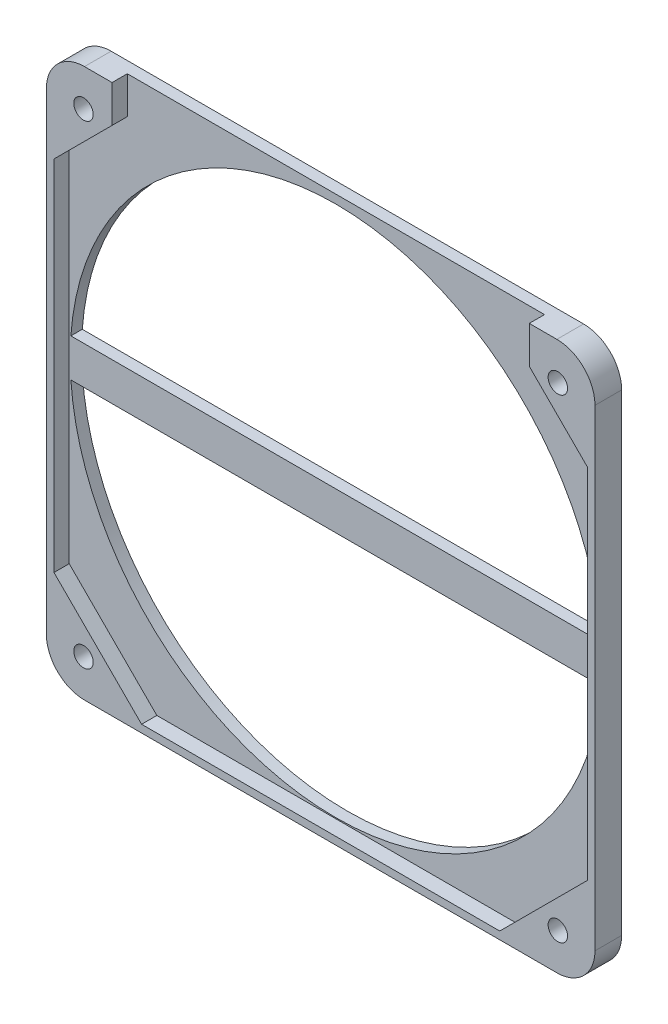
SolidWorks part; units mm, degrees
ref_plane "Přední rovina" through (0, 0, 0) normal (0, 0, 1) x (1, 0, 0)
ref_plane "Horní rovina" through (0, 0, 0) normal (0, 1, 0) x (1, 0, 0)
ref_plane "Pravá rovina" through (0, 0, 0) normal (1, 0, 0) x (0, 0, -1)
sketch "Skica1" plane through (0, 0, 0) normal (0, 0, 1) x (1, 0, 0)
  line L1 (-72, 72) -> (72, 72)
  line L2 (-72, 72) -> (-72, -72)
  line L3 (-72, -72) -> (72, -72)
  line L4 (72, 72) -> (72, -72)
  line L5 (-72, 72) -> (72, -72) construction
  line L6 (-72, -72) -> (72, 72) construction
  point P0 (0, 0)
  dimension "D1" = 144
  dimension "D2" = 144
extrude "Přidat vysunutím1" add sketch "Skica1" along normal blind 7
sketch "Skica2" plane through (0, 0, 7) normal (0, 0, 1) x (1, 0, 0)
  line L1 (-62.25, 62.25) -> (62.25, 62.25)
  line L2 (-62.25, 62.25) -> (-62.25, -62.25)
  line L3 (-62.25, -62.25) -> (62.25, -62.25)
  line L4 (62.25, 62.25) -> (62.25, -62.25)
  line L5 (-62.25, 62.25) -> (62.25, -62.25) construction
  line L6 (-62.25, -62.25) -> (62.25, 62.25) construction
  point P0 (0, 0)
  dimension "D1" = 124.5
  dimension "D2" = 124.5
hole_wizard "Díry pro kolík, velikost mm1" positions "Skica3" profile "Skica4" hole size "Ø5.0" standard "ANSI Metric"
sketch "Skica3" plane through (0, 0, 7) normal (0, 0, 1) x (1, 0, 0)
  point P0 (-62.25, -62.25)
  point P3 (-62.25, 62.25)
  point P6 (62.25, 62.25)
  point P9 (62.25, -62.25)
sketch "Skica4" plane through (-62.25, -62.25, 7) normal (1, 0, 0) x (0, -1, 0)
  line L0 (0, 0) -> (0, 6)
  line L1 (0, 6) -> (2.55, 6)
  line L2 (2.55, 6) -> (2.55, 0)
  line L5 (2.55, 0) -> (0, 0)
  line L10 (0, 6) -> (-2.55, 6) construction
  line L11 (0, -6.35) -> (0, 107.95) construction
  dimension "Průměr díry" = 5.1
  dimension "Hloubka díry" = 6
  dimension "Úhel vrtání" = 180
sketch "Skica5" plane through (0, 0, 7) normal (0, 0, 1) x (1, 0, 0)
  line L0 (-47, -70) -> (-70, -47)
  line L1 (-70, 70) -> (70, 70)
  line L2 (-70, 70) -> (-70, -70)
  line L3 (-70, -70) -> (70, -70)
  line L4 (70, 70) -> (70, -70)
  line L5 (-70, 70) -> (70, -70) construction
  line L6 (-70, -70) -> (70, 70) construction
  line L7 (-70, 47) -> (-47, 70)
  line L8 (47, 70) -> (70, 47)
  line L9 (70, -47) -> (47, -70)
  line L10 (-62.25, 62.25) -> (-58.5, 58.5)
  line L11 (-54.7523, 62.2477) -> (-54.7523, 72)
  line L12 (72, 72) -> (-72, 72) construction
  line L13 (0, 0) -> (0, 38.1754)
  line L14 (54.7523, 62.2477) -> (54.7523, 72)
  point P0 (0, 0)
  point P6 (-47, -70)
  point P11 (-54.7523, 62.2477)
  point P12 (0, 0)
  point P15 (0, 0)
  point P18 (0, 0)
  point P21 (0, 0)
  line M16 (72, 72) -> (-72, 72)
  dimension "D1" = 140
  dimension "D2" = 140
  dimension "D3" = 23
  dimension "D4" = 23
  dimension "D6" = 5.3
  dimension "D5" = 4
extrude "Odebrat vysunutím1" cut sketch "Skica5" against normal blind 4 contours L9 L4 L8 L1 L7 L2 L0 L3 | L11 L7 L1 | L1 L14 L11 M16 | L8 L14 L1
sketch "Skica6" plane through (0, 0, 3) normal (0, 0, 1) x (1, 0, 0)
  line L1 (-69.5706, 5) -> (69.5706, 5)
  line L2 (-69.5706, 5) -> (-69.5706, -5)
  line L3 (-69.5706, -5) -> (69.5706, -5)
  line L4 (69.5706, 5) -> (69.5706, -5)
  line L5 (-69.5706, 5) -> (69.5706, -5) construction
  line L6 (-69.5706, -5) -> (69.5706, 5) construction
  circle A0 centre (0, 0) radius 69.75
  dimension "D1" = 139.5
  dimension "D2" = 10
extrude "Odebrat vysunutím2" cut sketch "Skica6" against normal through all contours L1 A0 | L3 A0
fillet "Zaoblit1" radius 10 4 edges at (-72, -72, 3.5) (72, -72, 3.5) (72, 72, 3.5) (-72, 72, 3.5)
